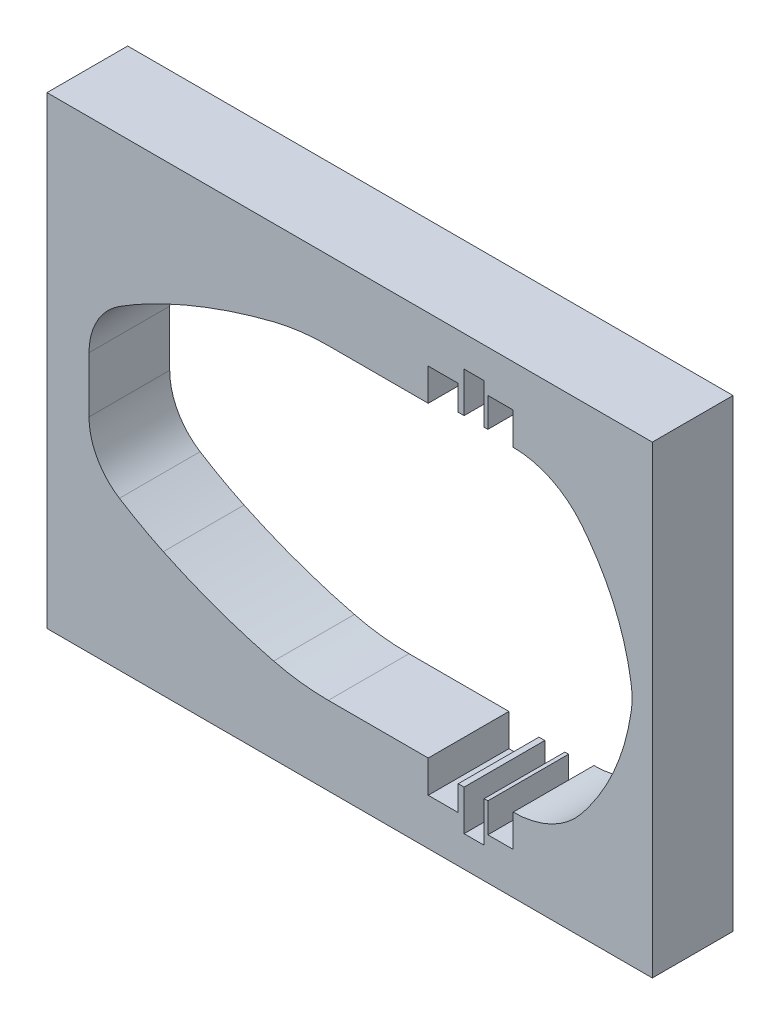
SolidWorks part; units mm, degrees
ref_plane "前基準面" through (0, 0, 0) normal (0, 0, 1) x (1, 0, 0)
ref_plane "上基準面" through (0, 0, 0) normal (0, 1, 0) x (1, 0, 0)
ref_plane "右基準面" through (0, 0, 0) normal (1, 0, 0) x (0, 0, -1)
sketch "草圖2" plane through (0, 0, 0) normal (0, 0, 1) x (1, 0, 0)
  line L0 (-46.4388, 70.8926) -> (220.2278, 70.8926) construction
  line L1 (-105.3201, 72.5991) -> (290.3658, 72.5991) construction
  line L2 (-47.2077, 65.7116) -> (-47.2077, 79.4866)
  line L3 (12.095, 110.6542) -> (33.772, 110.6542)
  line L4 (33.772, 110.6542) -> (36.8485, 110.6542)
  line L5 (36.8485, 110.6542) -> (36.8485, 118.6542)
  line L6 (36.8485, 118.6542) -> (44.2878, 118.6542)
  line L7 (44.2878, 118.6542) -> (44.2878, 112.451)
  line L8 (44.2878, 112.451) -> (45.736, 112.451)
  line L9 (45.736, 112.451) -> (45.736, 122.451)
  line L10 (45.736, 122.451) -> (50.7043, 122.451)
  line L11 (50.7043, 122.451) -> (50.7043, 112.451)
  line L12 (50.7043, 112.451) -> (51.628, 112.451)
  line L13 (51.628, 112.451) -> (51.628, 119.7465)
  line L14 (51.628, 119.7465) -> (57.8983, 119.7465)
  line L15 (57.8983, 119.7465) -> (57.8983, 111.7465)
  line L16 (87.0811, 75.9156) -> (87.1822, 75.2397)
  line L17 (87.0811, 69.2825) -> (87.1822, 69.9585)
  line L18 (57.8983, 25.4517) -> (57.8983, 33.4517)
  line L19 (51.628, 25.4517) -> (57.8983, 25.4517)
  line L20 (51.628, 32.7472) -> (51.628, 25.4517)
  line L21 (50.7043, 32.7472) -> (51.628, 32.7472)
  line L22 (50.7043, 22.7472) -> (50.7043, 32.7472)
  line L23 (45.736, 22.7472) -> (50.7043, 22.7472)
  line L24 (45.736, 32.7472) -> (45.736, 22.7472)
  line L25 (44.2878, 32.7472) -> (45.736, 32.7472)
  line L26 (44.2878, 26.544) -> (44.2878, 32.7472)
  line L27 (36.8485, 26.544) -> (44.2878, 26.544)
  line L28 (36.8485, 34.544) -> (36.8485, 26.544)
  line L29 (33.772, 34.544) -> (36.8485, 34.544)
  line L30 (12.095, 34.544) -> (33.772, 34.544)
  arc A0 (-47.2077, 79.4866) -> (-39.6723, 93.1805) centre (-30.9972, 79.4866) cw
  arc A1 (-39.6723, 93.1805) -> (-28.7843, 99.1911) centre (15.5612, 5.9932) cw
  arc A2 (-28.7843, 99.1911) -> (-1.443, 108.9923) centre (33.772, -32.279) cw
  arc A3 (-1.443, 108.9923) -> (12.095, 110.6542) centre (12.095, 54.6822) cw
  arc A4 (57.8983, 111.7465) -> (74.9109, 103.5094) centre (57.8983, 90.0594) cw
  arc A5 (74.9109, 103.5094) -> (76.7467, 101.0934) centre (12.9193, 54.4993) cw
  arc A6 (76.7467, 101.0934) -> (87.0811, 75.9156) centre (30.7128, 67.4885) cw
  arc A7 (87.1822, 75.2397) -> (87.1822, 69.9585) centre (69.5193, 72.5991) cw
  arc A8 (76.7467, 44.1048) -> (87.0811, 69.2825) centre (30.7128, 77.7096) ccw
  arc A9 (74.9109, 41.6888) -> (76.7467, 44.1048) centre (12.9193, 90.6989) ccw
  arc A10 (57.8983, 33.4517) -> (74.9109, 41.6888) centre (57.8983, 55.1388) ccw
  arc A11 (-1.443, 36.2059) -> (12.095, 34.544) centre (12.095, 90.516) ccw
  arc A12 (-28.7843, 46.0071) -> (-1.443, 36.2059) centre (33.772, 177.4772) ccw
  arc A13 (-39.6723, 52.0177) -> (-28.7843, 46.0071) centre (15.5612, 139.205) ccw
  arc A14 (-47.2077, 65.7116) -> (-39.6723, 52.0177) centre (-30.9972, 65.7116) ccw
  point P64 (-47.2077, 72.5991)
  dimension "D1" = 78.2948
  dimension "D2" = 1.0923
  dimension "D3" = 8
  dimension "D4" = 8
  dimension "D5" = 10
  dimension "D6" = 10
  dimension "D7" = 6.2704
  dimension "D8" = 7.4393
sketch "草圖4" plane through (0, 0, 0) normal (0, 0, 1) x (1, 0, 0)
  line L0 (-105.3201, 72.5991) -> (290.3658, 72.5991) construction
  line L1 (-57.6215, 130.0991) -> (92.3785, 130.0991)
  line L2 (-57.6215, 130.0991) -> (-57.6215, 15.0991)
  line L3 (-57.6215, 15.0991) -> (92.3785, 15.0991)
  line L4 (92.3785, 130.0991) -> (92.3785, 15.0991)
  arc A0 (87.1822, 69.9585) -> (87.1822, 75.2397) centre (69.5193, 72.5991) ccw construction
  point P9 (87.3785, 72.5991)
  dimension "D1" = 150
  dimension "D2" = 115
  dimension "D3" = 57.5
  dimension "D4" = 5
extrude "填料-伸長1" add sketch "草圖4" along normal blind 20 contours L4 L3 L2 L1
extrude "除料-伸長1" cut sketch "草圖2" along normal blind 20
ref_plane "平面1" through (-57.7, 0, 0) normal (1, 0, 0) x (0, 0, -1)
sketch "草圖6" plane through (-57.7, 0, 0) normal (1, 0, 0) x (0, 0, -1)
  line L0 (-10, 130.0991) -> (-10, 15.0991) construction
  line L1 (-20, 130.0991) -> (0, 130.0991) construction
  line L2 (-20, 15.0991) -> (0, 15.0991) construction
  line L3 (-20, 72.5991) -> (0, 72.5991) construction
  line L4 (-20, 130.0991) -> (-20, 15.0991) construction
  line L5 (0, 130.0991) -> (0, 15.0991) construction
  circle A0 centre (-10, 120.0991) radius 5
  circle A1 centre (-10, 105.0991) radius 5
  circle A2 centre (-10, 40.0991) radius 5
  circle A3 centre (-10, 25.0991) radius 5
  dimension "D1" = 10
  dimension "D2" = 5
  dimension "D5" = 5
sketch "草圖9" plane through (-57.7, 0, 0) normal (1, 0, 0) x (0, 0, -1)
  line L0 (-10, 130.0991) -> (-10, 15.0991) construction
  line L1 (-20, 72.5991) -> (0, 72.5991) construction
  circle A0 centre (-10, 90.0991) radius 5
  circle A1 centre (-10, 55.0991) radius 5
  circle A2 centre (-10, 105.0991) radius 5 construction
  dimension "D1" = 10
  dimension "D2" = 5
sketch "草圖11" plane through (-57.7, 0, 0) normal (1, 0, 0) x (0, 0, -1)
  line L0 (-10, 130.0991) -> (-10, 15.0991) construction
  circle A0 centre (-10, 72.5991) radius 5
  dimension "D1" = 10
extrude "除料-伸長7" cut sketch "草圖6" along normal blind 10
extrude "除料-伸長8" cut sketch "草圖9" along normal blind 5 contours A0 | A1
extrude "除料-伸長9" cut sketch "草圖11" along normal blind 5 contours A0
